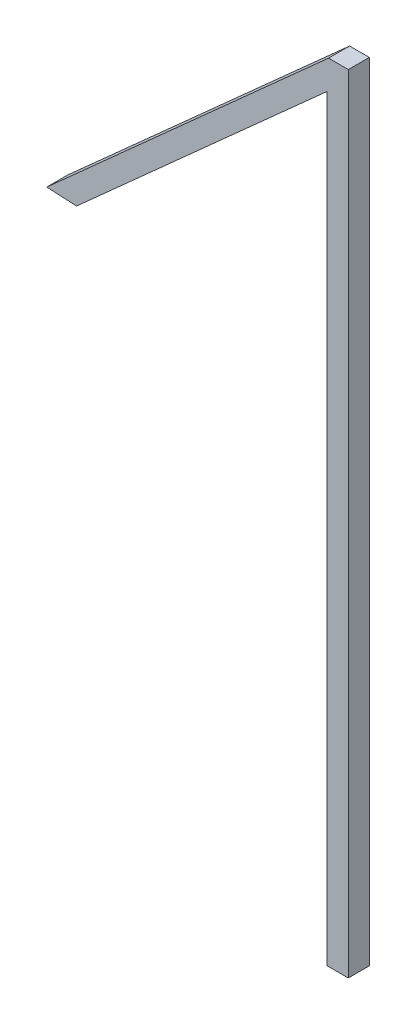
SolidWorks part; units mm, degrees
ref_plane "Front Plane" through (0, 0, 0) normal (0, 0, 1) x (1, 0, 0)
ref_plane "Top Plane" through (0, 0, 0) normal (0, 1, 0) x (1, 0, 0)
ref_plane "Right Plane" through (0, 0, 0) normal (1, 0, 0) x (0, 0, -1)
sketch "Sketch1" plane through (0, 0, 0) normal (0, 0, 1) x (1, 0, 0)
  line L0 (0.7104, 19.3615) -> (6.6682, 24.7005)
  line L1 (6.6682, 24.7005) -> (6.6682, 6.7005)
  line L2 (6.6682, 6.7005) -> (7.1682, 6.7005)
  line L3 (7.1682, 6.7005) -> (7.1682, 25.4)
  line L4 (7.1682, 25.4) -> (6.6996, 25.4)
  line L5 (6.6996, 25.4) -> (0, 19.3963)
  line L6 (0, 19.3963) -> (0.7104, 19.3615)
  dimension "D1" = 0.5
  dimension "D2" = 0.5
  dimension "D3" = 18
  dimension "D5" = 8
extrude "Boss-Extrude1" add sketch "Sketch1" along normal blind 0.5
